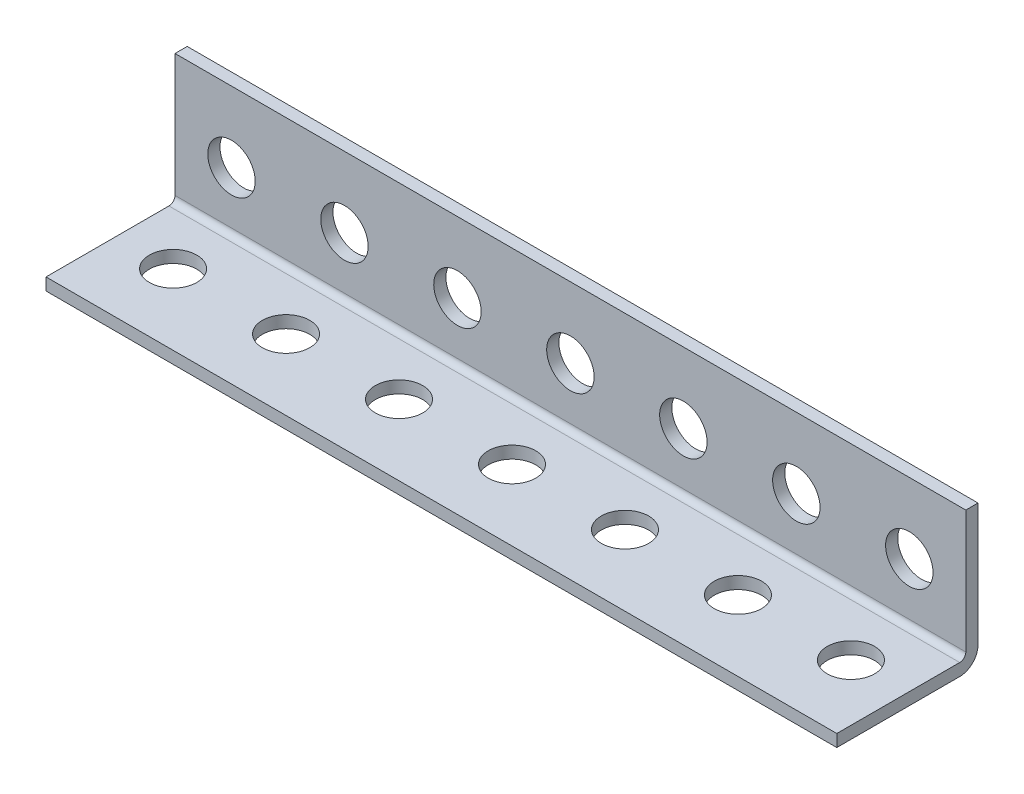
SolidWorks part; units mm, degrees
material "6061-T6 (SS)"
ref_plane "Front Plane" through (0, 0, 0) normal (0, 0, 1) x (1, 0, 0)
ref_plane "Top Plane" through (0, 0, 0) normal (0, 1, 0) x (1, 0, 0)
ref_plane "Right Plane" through (0, 0, 0) normal (1, 0, 0) x (0, 0, -1)
sketch "Sketch1" plane through (0, 0, 0) normal (1, 0, 0) x (0, 0, -1)
  line L0 (-15.875, -13.1318) -> (13.1318, -13.1318) construction
  line L1 (13.1318, -13.1318) -> (13.1318, 15.875) construction
  line L2 (13.1318, 15.875) -> (15.875, 15.875) construction
  line L3 (15.875, 15.875) -> (15.875, -15.875) construction
  line L4 (15.875, -15.875) -> (-15.875, -15.875) construction
  line L5 (-15.875, -15.875) -> (-15.875, -13.1318) construction
  line L6 (0, -15.875) -> (0, 15.875) construction
  line L7 (15.875, 0) -> (-15.875, 0) construction
  dimension "Thickness | T" = 2.7432
  dimension "Width (A)" = 31.75
  dimension "Width (B)" = 31.75
sketch "Sketch2" plane through (0, 0, 0) normal (0, 0, 1) x (1, 0, 0)
  line L0 (-609.6, 0) -> (609.6, 0) construction
  line L1 (-609.6, 15.875) -> (609.6, 15.875) construction
  line L2 (-609.6, 15.875) -> (-609.6, -15.875) construction
  line L3 (-609.6, -15.875) -> (609.6, -15.875) construction
  line L4 (609.6, 15.875) -> (609.6, -15.875) construction
  line L5 (0, 15.875) -> (0, -15.875) construction
  line L7 (-609.6, -13.1318) -> (609.6, -13.1318) construction
  circle A0 centre (596.9, 0) radius 5.334 construction
  circle A1 centre (571.5, 0) radius 5.334 construction
  point P15 (533.4, 0)
  point P16 (-533.4, 0)
  point P24 (602.234, 0)
  dimension "Mounting Hole Diameter" = 10.668
  dimension "Length | L" = 1219.2
  dimension "Mounting Hole Center to Center" = 25.4
  dimension "D1" = 12.7
  dimension "D2" = 63.5
sketch "Sketch3" plane through (0, 0, 0) normal (0, 1, 0) x (1, 0, 0)
  line L1 (-609.6, 15.875) -> (609.6, 15.875) construction
  line L2 (-609.6, 15.875) -> (-609.6, -15.875) construction
  line L3 (-609.6, -15.875) -> (609.6, -15.875) construction
  line L4 (609.6, 15.875) -> (609.6, -15.875) construction
  line L5 (-609.6, 13.1318) -> (609.6, 13.1318) construction
  line L7 (-609.6, 0) -> (609.6, 0) construction
  circle A0 centre (596.9, 0) radius 5.334 construction
  circle A1 centre (571.5, 0) radius 5.334 construction
  point P19 (-533.4, 0)
  point P21 (602.234, 0)
  point P22 (533.4, 0)
sketch "Sketch4" plane through (0, 0, 0) normal (1, 0, 0) x (0, 0, -1)
  line L0 (-15.875, -13.1318) -> (11.7602, -13.1318)
  line L1 (13.1318, -11.7602) -> (13.1318, 15.875)
  line L2 (13.1318, 15.875) -> (15.875, 15.875)
  line L3 (15.875, 15.875) -> (15.875, -11.7602)
  line L4 (11.7602, -15.875) -> (-15.875, -15.875)
  line L5 (-15.875, -15.875) -> (-15.875, -13.1318)
  line L6 (11.7602, -13.1318) -> (11.7602, -10.3886) construction
  arc A0 (11.7602, -13.1318) -> (13.1318, -11.7602) centre (11.7602, -11.7602) ccw
  arc A1 (15.875, -11.7602) -> (11.7602, -15.875) centre (11.7602, -11.7602) cw
extrude "Boss-Extrude1" add sketch "Sketch4" along normal up to vertex (609.6 mm away) and the other way up to vertex (609.6 mm away) up to point (609.6, 0, 0) other way up to point (-609.6, 0, 0)
sketch "Sketch5" plane through (0, 0, 0) normal (0, 0, 1) x (1, 0, 0)
  circle A0 centre (596.9, 0) radius 5.334
extrude "Cut-Extrude1" cut sketch "Sketch5" against normal through all
sketch "Sketch6" plane through (0, 0, 0) normal (0, 1, 0) x (1, 0, 0)
  circle A0 centre (596.9, 0) radius 5.334
extrude "Cut-Extrude2" cut sketch "Sketch6" against normal through all
pattern_linear "LPattern1" count 48 spacing 25.4 along (-1, 0, 0) of "Cut-Extrude2", "Cut-Extrude1"
sketch "Sketch7" plane through (0, 0, -15.875) normal (0, 0, -1) x (-1, 0, 0)
  line L0 (-609.6, -15.875) -> (609.6, -15.875) construction
  line L1 (-609.6, 15.875) -> (25.4, 15.875)
  line L2 (-609.6, 15.875) -> (-609.6, -15.875)
  line L3 (-609.6, -15.875) -> (25.4, -15.875)
  line L4 (25.4, 15.875) -> (25.4, -15.875)
  line L5 (602.234, 0) -> (609.6, 0) construction
  line L6 (609.6, -11.7602) -> (609.6, 15.875) construction
  line L7 (32.766, 0) -> (25.4, 0)
  circle A0 centre (596.9, 0) radius 5.334 construction
  circle A1 centre (38.1, 0) radius 5.334 construction
  dimension "D1" = 7.366
extrude "Cut-Extrude3" cut sketch "Sketch7" against normal blind 70 contours L4 L1 L2 L3
sketch "Sketch8" plane through (0, 0, -15.875) normal (0, 0, -1) x (-1, 0, 0)
  line L0 (25.4, -15.875) -> (609.6, -15.875) construction
  line L1 (25.4, 15.875) -> (50.8, 15.875)
  line L2 (25.4, 15.875) -> (25.4, -15.875)
  line L3 (25.4, -15.875) -> (50.8, -15.875)
  line L4 (50.8, 15.875) -> (50.8, -15.875)
  line L6 (58.166, 0) -> (50.8, 0)
  circle A0 centre (63.5, 0) radius 5.334 construction
  circle M28 centre (38.1, 0) radius 5.334
  line M29 (25.4, 15.875) -> (25.4, -11.7602)
  line M30 (25.4, -11.7602) -> (609.6, -11.7602)
  line M32 (609.6, 15.875) -> (25.4, 15.875)
  dimension "D1" = 7.366
extrude "Cut-Extrude4" cut sketch "Sketch8" against normal blind 70 contours L4 M32 M29 M30 M28 | L4 L2 L3 M30
sketch "Sketch9" plane through (0, 0, -15.875) normal (0, 0, -1) x (-1, 0, 0)
  line L0 (50.8, -15.875) -> (609.6, -15.875) construction
  line L1 (50.8, 15.875) -> (431.8, 15.875)
  line L2 (50.8, 15.875) -> (50.8, -15.875)
  line L3 (50.8, -15.875) -> (431.8, -15.875)
  line L4 (431.8, 15.875) -> (431.8, -15.875)
  line L5 (439.166, 0) -> (431.8, 0)
  circle A0 centre (444.5, 0) radius 5.334 construction
  circle M7 centre (63.5, 0) radius 5.334
  circle M8 centre (88.9, 0) radius 5.334
  circle M9 centre (114.3, 0) radius 5.334
  circle M10 centre (139.7, 0) radius 5.334
  circle M11 centre (165.1, 0) radius 5.334
  circle M12 centre (190.5, 0) radius 5.334
  circle M13 centre (215.9, 0) radius 5.334
  circle M14 centre (241.3, 0) radius 5.334
  circle M15 centre (266.7, 0) radius 5.334
  circle M16 centre (292.1, 0) radius 5.334
  circle M17 centre (317.5, 0) radius 5.334
  circle M18 centre (342.9, 0) radius 5.334
  circle M19 centre (368.3, 0) radius 5.334
  circle M20 centre (393.7, 0) radius 5.334
  circle M21 centre (419.1, 0) radius 5.334
  line M29 (50.8, 15.875) -> (50.8, -11.7602)
  line M30 (50.8, -11.7602) -> (609.6, -11.7602)
  line M32 (609.6, 15.875) -> (50.8, 15.875)
  dimension "7.366" = 7.366
extrude "Cut-Extrude5" cut sketch "Sketch9" against normal blind 70 contours L4 M32 M29 M30 M8 M10 M12 M14 M16 M18 M20 M21 M19 M17 M15 M13 M11 M9 M7 | L4 L2 L3 M30
sketch "Sketch10" plane through (0, 0, -15.875) normal (0, 0, -1) x (-1, 0, 0)
  line L0 (439.166, 0) -> (431.8, 0)
  line L1 (431.8, 15.875) -> (431.8, -11.7602) construction
  line L2 (444.5, 5.334) -> (444.5, 15.875)
  line L3 (431.8, 15.875) -> (609.6, 15.875) construction
  line L4 (602.234, 0) -> (609.6, 0)
  line L5 (609.6, -11.7602) -> (609.6, 15.875) construction
  line L6 (596.9, 5.334) -> (596.9, 15.875)
  circle A0 centre (444.5, 0) radius 5.334 construction
  circle A1 centre (596.9, 0) radius 5.334 construction
sketch "Sketch11" plane through (0, -15.875, 0) normal (0, -1, 0) x (1, 0, 0)
  line L0 (-602.234, 0) -> (-609.6, 0)
  line L1 (-609.6, 15.875) -> (-609.6, -11.7602) construction
  line L2 (-596.9, 5.334) -> (-596.9, 15.875)
  line L3 (-431.8, 15.875) -> (-609.6, 15.875) construction
  line L4 (-439.166, 0) -> (-431.8, 0)
  line L5 (-431.8, 15.875) -> (-431.8, -11.7602) construction
  line L6 (-444.5, 5.334) -> (-444.5, 15.875)
  circle A0 centre (-596.9, 0) radius 5.334 construction
  circle A1 centre (-444.5, 0) radius 5.334 construction
equation "\"D1@Sketch2\"= ( \"Length | L@Sketch2\" - \"Mounting Hole Center to Center@Sketch2\" * \"Num Holes\" ) / 2"
equation "\"Num Holes\"= int ( \"Length | L@Sketch2\" / \"Mounting Hole Center to Center@Sketch2\" ) - 1"
equation "\"D2@Sketch2\"=\"Mounting Hole Center to Center@Sketch2\"*2.5"
equation "\"D3@LPattern1\"=\"Mounting Hole Center to Center@Sketch2\""
